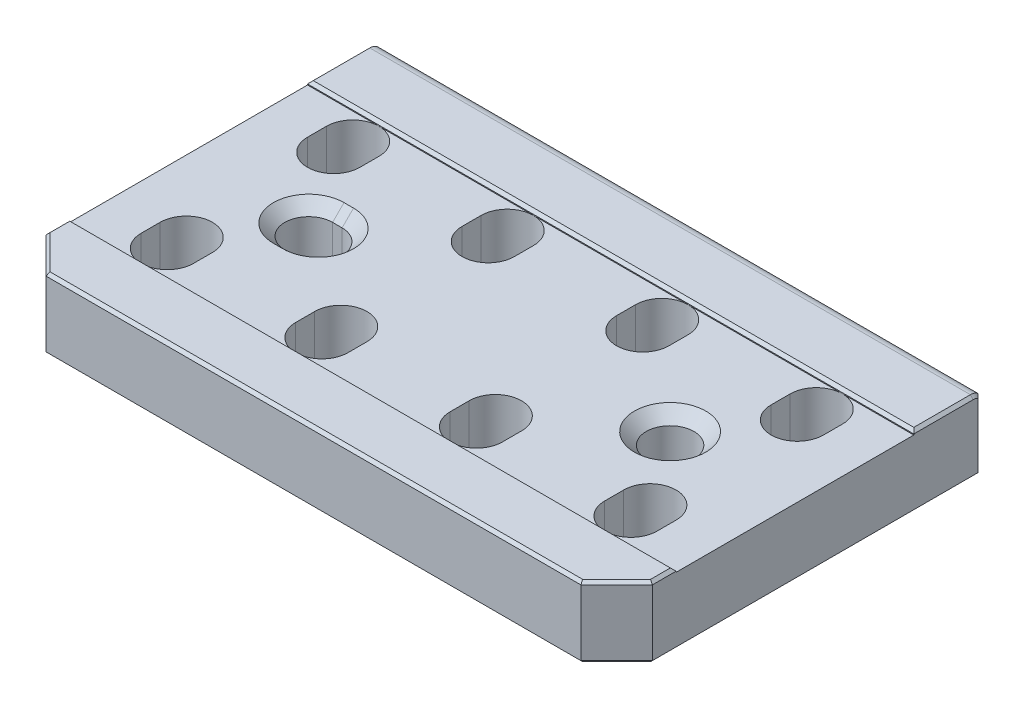
SolidWorks part; units mm, degrees
material "17-4 PH SSTL, H 1150"
ref_plane "Front" through (0, 0, 0) normal (0, 0, 1) x (1, 0, 0)
ref_plane "Top" through (0, 0, 0) normal (0, 1, 0) x (1, 0, 0)
ref_plane "Right" through (0, 0, 0) normal (1, 0, 0) x (0, 0, -1)
sketch "Sketch1" plane through (0, 0, 0) normal (1, 0, 0) x (0, 0, -1)
  line L1 (-47.625, 0) -> (47.625, 0)
  line L2 (-47.625, 0) -> (-47.625, 19.05)
  line L3 (-47.625, 19.05) -> (47.625, 19.05)
  line L4 (47.625, 0) -> (47.625, 19.05)
  dimension "D1" = 19.05
  dimension "D2" = 95.25
extrude "Extrude1" add sketch "Sketch1" along normal mid plane 161.925
chamfer "Chamfer1" distance 9.525 angle 45 2 edges at (-80.9625, 9.525, 47.625) (80.9625, 9.525, 47.625)
sketch "Sketch6" plane through (0, 19.05, 0) normal (0, 1, 0) x (1, 0, 0)
  line L0 (-80.9625, 47.625) -> (-80.9625, -38.1) construction
  line L1 (-80.9625, 31.75) -> (80.9625, 31.75)
  line L5 (80.9625, 47.625) -> (80.9625, -38.1) construction
  line L8 (-80.9625, 31.75) -> (-80.9625, -31.75)
  line L9 (-80.9625, -31.75) -> (80.9625, -31.75)
  line L10 (80.9625, -31.75) -> (80.9625, 31.75)
  dimension "D1" = 31.75
  dimension "D2" = 31.75
extrude "Extrude2" cut sketch "Sketch6" against normal blind 1.016
sketch "Sketch10" plane through (0, 0, 0) normal (1, 0, 0) x (0, 0, -1)
  line L0 (47.117, 19.05) -> (47.117, 0)
  line L2 (47.117, 0) -> (49.657, 0)
  line L3 (49.657, 0) -> (49.657, 18.3146)
  line L4 (47.625, 19.05) -> (47.117, 19.05)
  arc A1 (49.657, 18.3146) -> (47.625, 19.05) centre (47.625, 15.875) ccw
  dimension "D1" = 3.175
extrude "Extrude5" add sketch "Sketch10" against normal mid plane 161.925
sketch "Sketch16" plane through (0, 0, 0) normal (0, -1, 0) x (1, 0, 0)
  line L0 (-61.9125, 24.765) -> (-61.9125, 19.685) construction
  line L1 (-54.9275, 24.765) -> (-54.9275, 19.685)
  line L2 (-68.8975, 24.765) -> (-68.8975, 19.685)
  line L3 (-61.9125, 22.225) -> (-20.6375, 22.225) construction
  line L4 (-20.6375, 22.225) -> (20.6375, 22.225) construction
  line L5 (20.6375, 22.225) -> (61.9125, 22.225) construction
  line L6 (-61.9125, -19.685) -> (-61.9125, -24.765) construction
  line L7 (-54.9275, -19.685) -> (-54.9275, -24.765)
  line L8 (-68.8975, -19.685) -> (-68.8975, -24.765)
  line L9 (80.9625, -47.625) -> (-80.9625, -47.625) construction
  line L10 (-20.6375, -19.685) -> (-20.6375, -24.765) construction
  line L11 (-13.6525, -19.685) -> (-13.6525, -24.765)
  line L12 (-27.6225, -19.685) -> (-27.6225, -24.765)
  line L13 (20.6375, -19.685) -> (20.6375, -24.765) construction
  line L14 (27.6225, -19.685) -> (27.6225, -24.765)
  line L15 (13.6525, -19.685) -> (13.6525, -24.765)
  line L16 (61.9125, -19.685) -> (61.9125, -24.765) construction
  line L17 (68.8975, -19.685) -> (68.8975, -24.765)
  line L18 (54.9275, -19.685) -> (54.9275, -24.765)
  line L19 (61.9125, 24.765) -> (61.9125, 19.685) construction
  line L20 (68.8975, 24.765) -> (68.8975, 19.685)
  line L21 (54.9275, 24.765) -> (54.9275, 19.685)
  line L22 (20.6375, 24.765) -> (20.6375, 19.685) construction
  line L23 (27.6225, 24.765) -> (27.6225, 19.685)
  line L24 (13.6525, 24.765) -> (13.6525, 19.685)
  line L25 (-20.6375, 24.765) -> (-20.6375, 19.685) construction
  line L26 (-13.6525, 24.765) -> (-13.6525, 19.685)
  line L27 (-27.6225, 24.765) -> (-27.6225, 19.685)
  arc A0 (-54.9275, 24.765) -> (-68.8975, 24.765) centre (-61.9125, 24.765) ccw
  arc A1 (-68.8975, 19.685) -> (-54.9275, 19.685) centre (-61.9125, 19.685) ccw
  arc A2 (-54.9275, -19.685) -> (-68.8975, -19.685) centre (-61.9125, -19.685) ccw
  arc A3 (-68.8975, -24.765) -> (-54.9275, -24.765) centre (-61.9125, -24.765) ccw
  arc A4 (-13.6525, -19.685) -> (-27.6225, -19.685) centre (-20.6375, -19.685) ccw
  arc A5 (-27.6225, -24.765) -> (-13.6525, -24.765) centre (-20.6375, -24.765) ccw
  arc A6 (27.6225, -19.685) -> (13.6525, -19.685) centre (20.6375, -19.685) ccw
  arc A7 (13.6525, -24.765) -> (27.6225, -24.765) centre (20.6375, -24.765) ccw
  arc A8 (68.8975, -19.685) -> (54.9275, -19.685) centre (61.9125, -19.685) ccw
  arc A9 (54.9275, -24.765) -> (68.8975, -24.765) centre (61.9125, -24.765) ccw
  arc A10 (68.8975, 24.765) -> (54.9275, 24.765) centre (61.9125, 24.765) ccw
  arc A11 (54.9275, 19.685) -> (68.8975, 19.685) centre (61.9125, 19.685) ccw
  arc A12 (27.6225, 24.765) -> (13.6525, 24.765) centre (20.6375, 24.765) ccw
  arc A13 (13.6525, 19.685) -> (27.6225, 19.685) centre (20.6375, 19.685) ccw
  arc A14 (-13.6525, 24.765) -> (-27.6225, 24.765) centre (-20.6375, 24.765) ccw
  arc A15 (-27.6225, 19.685) -> (-13.6525, 19.685) centre (-20.6375, 19.685) ccw
  point P2 (-61.9125, 22.225)
  point P9 (0, 22.225)
  point P15 (-61.9125, -22.225)
  point P24 (-20.6375, -22.225)
  point P29 (20.6375, -22.225)
  point P36 (61.9125, -22.225)
  point P43 (61.9125, 22.225)
  point P50 (20.6375, 22.225)
  point P57 (-20.6375, 22.225)
  dimension "D1" = 13.97
  dimension "D2" = 5.08
  dimension "D3" = 44.45
  dimension "D4" = 25.4
  dimension "D5" = 41.275
extrude "Extrude8" cut sketch "Sketch16" against normal through all
chamfer "Chamfer8" distance 0.762 angle 45 32 edges at (61.9125, 0, -12.7) (54.9275, 0, -22.225) (68.8975, 0, -22.225) (61.9125, 0, -31.75) (61.9125, 0, 31.75) (54.9275, 0, 22.225) (68.8975, 0, 22.225) (61.9125, 0, 12.7) (20.6375, 0, 31.75) (13.6525, 0, 22.225) (27.6225, 0, 22.225) (20.6375, 0, 12.7) (20.6375, 0, -12.7) (13.6525, 0, -22.225) (27.6225, 0, -22.225) (20.6375, 0, -31.75) (-20.6375, 0, -12.7) (-27.6225, 0, -22.225) (-13.6525, 0, -22.225) (-20.6375, 0, -31.75) (-20.6375, 0, 31.75) (-27.6225, 0, 22.225) (-13.6525, 0, 22.225) (-20.6375, 0, 12.7) (-61.9125, 0, 31.75) (-68.8975, 0, 22.225) (-54.9275, 0, 22.225) (-61.9125, 0, 12.7) (-61.9125, 0, -12.7) (-68.8975, 0, -22.225) (-54.9275, 0, -22.225) (-61.9125, 0, -31.75)
hole_wizard "1/2 (0.5) Diameter Hole2" positions "Sketch18" profile "Sketch17" hole size "1/2" standard "Ansi Inch" end condition through all
sketch "Sketch18" plane through (20.4521, 18.034, -42.2516) normal (0, -1, 0) x (1, 0, 0)
  line L0 (-9.9746, 42.2516) -> (-30.9296, 42.2516) construction
  line L1 (-20.4521, 42.2516) -> (-20.4521, 42.2119) construction
  point P0 (27.1729, 42.2516)
  dimension "D1" = 95.25
sketch "Sketch17" plane through (47.625, 18.034, 0) normal (1, 0, 0) x (0, 0, 1)
  line L0 (0, 0) -> (0, 18.034)
  line L1 (0, 18.034) -> (9.525, 18.034)
  line L2 (6.3754, 14.8844) -> (6.3754, 3.1496)
  line L3 (6.3754, 3.1496) -> (9.525, 0)
  line L5 (9.525, 0) -> (0, 0)
  line L6 (-6.3754, 3.1496) -> (-9.525, 0) construction
  line L7 (9.525, 18.034) -> (6.3754, 14.8844)
  line L8 (-9.525, 18.034) -> (-6.3754, 14.8844) construction
  line L11 (0, -6.35) -> (0, 107.95) construction
  dimension "Thru Hole Dia." = 12.7508
  dimension "Thru Hole Depth" = 18.034
  dimension "Near C'Sink Dia." = 19.05
  dimension "Near C'Sink Angle" = 90
  dimension "Far C'Sink Dia." = 19.05
  dimension "Far C'Sink Angle" = 90
sketch "Sketch20" plane through (0, 18.034, 0) normal (0, 1, 0) x (1, 0, 0)
  line L0 (-48.895, 6.3754) -> (-46.355, 6.3754)
  line L1 (-48.895, -6.3754) -> (-46.355, -6.3754)
  line L2 (47.625, 0) -> (-46.355, 0) construction
  line L3 (-46.355, 0) -> (-48.895, 0) construction
  arc A0 (-46.355, -6.3754) -> (-46.355, 6.3754) centre (-46.355, 0) ccw
  arc A1 (-48.895, 6.3754) -> (-48.895, -6.3754) centre (-48.895, 0) ccw
  circle A2 centre (47.625, 0) radius 6.3754 construction
  dimension "D1" = 93.98
  dimension "D2" = 2.54
extrude "Extrude9" cut sketch "Sketch20" against normal through all
chamfer "Chamfer9" distance 3.048 angle 45 8 edges at (-47.625, 0, 6.3754) (-55.2704, 0, 0) (-47.625, 0, -6.3754) (-39.9796, 0, 0) (-55.2704, 18.034, 0) (-47.625, 18.034, -6.3754) (-47.625, 18.034, 6.3754) (-39.9796, 18.034, 0)
chamfer "Chamfer6" distance 0.762 angle 45 19 edges at (0, 0, -49.657) (76.2, 19.05, 42.8625) (0, 19.05, 47.625) (-76.2, 19.05, 42.8625) (-80.9625, 19.05, 34.925) (0, 19.05, 31.75) (80.9625, 19.05, 34.925) (80.9625, 18.8605, -48.7055) (-80.9625, 18.8605, -48.7055) (-80.9625, 19.05, -39.6875) (80.9625, 19.05, -39.6875) (80.9625, 9.1573, -49.657) (-80.9625, 9.1573, -49.657) (-80.9625, 0, -5.7785) (-76.2, 0, 42.8625) (0, 0, 47.625) (76.2, 0, 42.8625) (80.9625, 0, -5.7785) (0, 19.05, -31.75)
